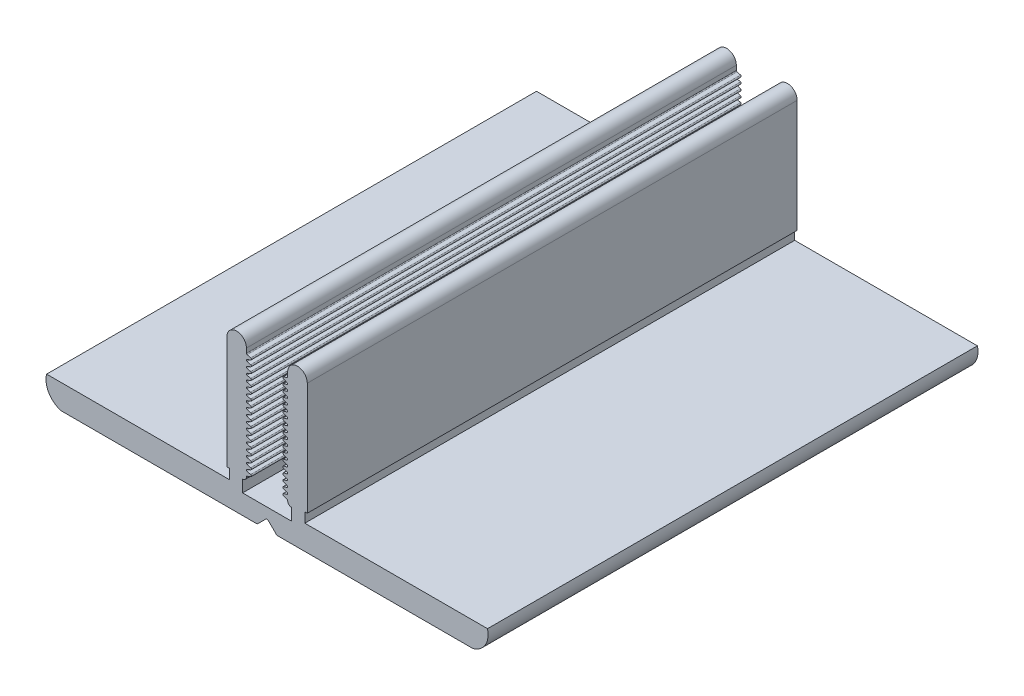
SolidWorks part; units mm, degrees
ref_plane "Спереди" through (0, 0, 0) normal (0, 0, 1) x (1, 0, 0)
ref_plane "Сверху" through (0, 0, 0) normal (0, 1, 0) x (1, 0, 0)
ref_plane "Справа" through (0, 0, 0) normal (1, 0, 0) x (0, 0, -1)
sketch "Эскиз1" plane through (0, 0, 0) normal (0, 0, 1) x (1, 0, 0)
  line L12 (1.5975, 2) -> (6.5975, 2)
  line L80 (3.9561, 0.8586) -> (3.1561, 0.0586)
  line L100 (2.0661, 10.8085) -> (2.4215, 10.7114)
  line L101 (2.0604, 10.384) -> (2.43, 10.5212)
  line L102 (2.0604, 10.9909) -> (2.43, 11.1281)
  line L104 (2.0604, 12.8116) -> (2.43, 12.9488)
  line L105 (2.0661, 11.4154) -> (2.4215, 11.3183)
  line L107 (3.0147, 0) -> (-9.305, 0)
  line L108 (2.0661, 7.774) -> (2.4215, 7.6769)
  line L109 (2.0604, 7.9564) -> (2.43, 8.0936)
  line L110 (2.0661, 8.3809) -> (2.4215, 8.2838)
  line L111 (2.0661, 10.2016) -> (2.4215, 10.1045)
  line L112 (2.0661, 8.9878) -> (2.4215, 8.8907)
  line L113 (2.0604, 8.5633) -> (2.43, 8.7005)
  line L114 (2.0604, 9.1702) -> (2.43, 9.3074)
  line L115 (2.0604, 9.7771) -> (2.43, 9.9143)
  line L116 (2.0661, 9.5947) -> (2.4215, 9.4976)
  line L117 (2.0661, 4.1326) -> (2.4215, 4.0355)
  line L118 (2.0604, 3.7081) -> (2.43, 3.8453)
  line L119 (2.0604, 4.315) -> (2.43, 4.4522)
  line L120 (2.0661, 4.7395) -> (2.4215, 4.6424)
  line L121 (2.0661, 5.3464) -> (2.4215, 5.2493)
  line L122 (2.0604, 5.5288) -> (2.43, 5.666)
  line L123 (2.0661, 5.9533) -> (2.4215, 5.8562)
  line L124 (2.0604, 4.9219) -> (2.43, 5.0591)
  line L125 (2.0661, 6.5602) -> (2.4215, 6.4631)
  line L126 (2.0604, 6.7426) -> (2.43, 6.8798)
  line L127 (2.0604, 6.1357) -> (2.43, 6.2729)
  line L128 (2.0604, 7.3495) -> (2.43, 7.4867)
  line L129 (2.0661, 7.1671) -> (2.4215, 7.07)
  line L130 (1.5975, 3.22) -> (1.5975, 2)
  line L131 (-0.0073, 3.5056) -> (0.2427, 3.5056)
  line L132 (0.2427, 3.5056) -> (0.2427, 2.5)
  line L135 (-0.0073, 3.5056) -> (-0.0073, 15)
  line L136 (2.0604, 13.4185) -> (2.43, 13.5557)
  line L138 (-16.9025, 0) -> (-9.305, 0)
  line L140 (2.0661, 13.843) -> (2.4215, 13.7459)
  line L141 (1.9927, 15) -> (1.9927, 14.5393)
  line L142 (2.0661, 12.0223) -> (2.4215, 11.9252)
  line L143 (2.0661, 14.4499) -> (2.4215, 14.3528)
  line L144 (2.0604, 14.0254) -> (2.43, 14.1626)
  line L145 (2.0604, 11.5978) -> (2.43, 11.735)
  line L146 (2.0661, 12.6292) -> (2.4215, 12.5321)
  line L147 (2.0661, 13.2361) -> (2.4215, 13.139)
  line L148 (2.0604, 12.2047) -> (2.43, 12.3419)
  line L149 (4.2389, 0.8586) -> (5.0389, 0.0586)
  line L150 (6.1346, 12.2047) -> (5.765, 12.3419)
  line L151 (6.1289, 13.2361) -> (5.7735, 13.139)
  line L152 (6.1289, 12.6292) -> (5.7735, 12.5321)
  line L153 (6.1346, 11.5978) -> (5.765, 11.735)
  line L154 (6.1346, 14.0254) -> (5.765, 14.1626)
  line L155 (6.1289, 14.4499) -> (5.7735, 14.3528)
  line L156 (6.1289, 12.0223) -> (5.7735, 11.9252)
  line L157 (6.2023, 15) -> (6.2023, 14.5393)
  line L158 (6.1289, 13.843) -> (5.7735, 13.7459)
  line L159 (6.1346, 13.4185) -> (5.765, 13.5557)
  line L160 (8.2023, 3.5056) -> (8.2023, 15)
  line L161 (7.9523, 3.5056) -> (7.9523, 2.5)
  line L162 (8.2023, 3.5056) -> (7.9523, 3.5056)
  line L163 (6.5975, 3.22) -> (6.5975, 2)
  line L164 (6.1289, 7.1671) -> (5.7735, 7.07)
  line L165 (6.1346, 7.3495) -> (5.765, 7.4867)
  line L166 (6.1346, 6.1357) -> (5.765, 6.2729)
  line L167 (6.1346, 6.7426) -> (5.765, 6.8798)
  line L168 (6.1289, 6.5602) -> (5.7735, 6.4631)
  line L169 (6.1346, 4.9219) -> (5.765, 5.0591)
  line L170 (6.1289, 5.9533) -> (5.7735, 5.8562)
  line L171 (6.1346, 5.5288) -> (5.765, 5.666)
  line L172 (6.1289, 5.3464) -> (5.7735, 5.2493)
  line L173 (6.1289, 4.7395) -> (5.7735, 4.6424)
  line L174 (6.1346, 4.315) -> (5.765, 4.4522)
  line L175 (6.1346, 3.7081) -> (5.765, 3.8453)
  line L176 (6.1289, 4.1326) -> (5.7735, 4.0355)
  line L177 (6.1289, 9.5947) -> (5.7735, 9.4976)
  line L178 (6.1346, 9.7771) -> (5.765, 9.9143)
  line L179 (6.1346, 9.1702) -> (5.765, 9.3074)
  line L180 (6.1346, 8.5633) -> (5.765, 8.7005)
  line L181 (6.1289, 8.9878) -> (5.7735, 8.8907)
  line L182 (6.1289, 10.2016) -> (5.7735, 10.1045)
  line L183 (6.1289, 8.3809) -> (5.7735, 8.2838)
  line L184 (6.1346, 7.9564) -> (5.765, 8.0936)
  line L185 (6.1289, 7.774) -> (5.7735, 7.6769)
  line L187 (6.1289, 11.4154) -> (5.7735, 11.3183)
  line L188 (6.1346, 12.8116) -> (5.765, 12.9488)
  line L189 (6.1346, 10.9909) -> (5.765, 11.1281)
  line L190 (6.1346, 10.384) -> (5.765, 10.5212)
  line L191 (6.1289, 10.8085) -> (5.7735, 10.7114)
  line L192 (25.0975, 0) -> (17.5, 0)
  line L195 (5.1803, 0) -> (17.5, 0)
  line L197 (10.7643, 2.5) -> (7.9523, 2.5)
  line L198 (10.7643, 2.5) -> (26.5975, 2.5)
  line L199 (0.2427, 2.5) -> (-18.4025, 2.5)
  arc A91 (4.2389, 0.8586) -> (3.9561, 0.8586) centre (4.0975, 0.7172) ccw
  arc A94 (2.43, 3.8453) -> (2.4215, 4.0355) centre (2.3952, 3.939) ccw
  arc A95 (2.43, 4.4522) -> (2.4215, 4.6424) centre (2.3952, 4.5459) ccw
  arc A96 (2.43, 5.0591) -> (2.4215, 5.2493) centre (2.3952, 5.1528) ccw
  arc A97 (3.0147, 0) -> (3.1561, 0.0586) centre (3.0147, 0.2) ccw
  arc A98 (2.43, 7.4867) -> (2.4215, 7.6769) centre (2.3952, 7.5804) ccw
  arc A99 (2.43, 8.0936) -> (2.4215, 8.2838) centre (2.3952, 8.1873) ccw
  arc A100 (1.9927, 10.8979) -> (2.0604, 10.9909) centre (2.0965, 10.8935) cw
  arc A101 (2.43, 10.5212) -> (2.4215, 10.7114) centre (2.3952, 10.6149) ccw
  arc A102 (2.0661, 10.8085) -> (1.9927, 10.8979) centre (2.0924, 10.905) cw
  arc A103 (2.43, 9.9143) -> (2.4215, 10.1045) centre (2.3952, 10.008) ccw
  arc A104 (2.43, 9.3074) -> (2.4215, 9.4976) centre (2.3952, 9.4011) ccw
  arc A105 (2.43, 8.7005) -> (2.4215, 8.8907) centre (2.3952, 8.7942) ccw
  arc A106 (2.0661, 11.4154) -> (1.9927, 11.5048) centre (2.0924, 11.5119) cw
  arc A107 (2.43, 11.1281) -> (2.4215, 11.3183) centre (2.3952, 11.2218) ccw
  arc A108 (2.43, 5.666) -> (2.4215, 5.8562) centre (2.3952, 5.7597) ccw
  arc A109 (2.43, 6.2729) -> (2.4215, 6.4631) centre (2.3952, 6.3666) ccw
  arc A110 (2.43, 6.8798) -> (2.4215, 7.07) centre (2.3952, 6.9735) ccw
  arc A113 (2.0661, 7.774) -> (1.9927, 7.8634) centre (2.0924, 7.8705) cw
  arc A114 (2.0661, 8.3809) -> (1.9927, 8.4703) centre (2.0924, 8.4774) cw
  arc A115 (1.9927, 7.8634) -> (2.0604, 7.9564) centre (2.0965, 7.859) cw
  arc A116 (2.0661, 9.5947) -> (1.9927, 9.6841) centre (2.0924, 9.6912) cw
  arc A117 (2.0661, 8.9878) -> (1.9927, 9.0772) centre (2.0924, 9.0843) cw
  arc A118 (1.9927, 9.0772) -> (2.0604, 9.1702) centre (2.0965, 9.0728) cw
  arc A119 (2.0661, 10.2016) -> (1.9927, 10.291) centre (2.0924, 10.2981) cw
  arc A120 (1.9927, 8.4703) -> (2.0604, 8.5633) centre (2.0965, 8.4659) cw
  arc A121 (1.9927, 10.291) -> (2.0604, 10.384) centre (2.0965, 10.2866) cw
  arc A122 (1.9927, 9.6841) -> (2.0604, 9.7771) centre (2.0965, 9.6797) cw
  arc A123 (1.9927, 3.6152) -> (1.5975, 3.22) centre (1.5975, 3.6152) cw
  arc A124 (2.0661, 4.1326) -> (1.9927, 4.2221) centre (2.0924, 4.2291) cw
  arc A125 (1.9927, 3.6152) -> (2.0604, 3.7081) centre (2.0965, 3.6107) cw
  arc A126 (1.9927, 4.2221) -> (2.0604, 4.315) centre (2.0965, 4.2176) cw
  arc A127 (2.0661, 4.7395) -> (1.9927, 4.829) centre (2.0924, 4.836) cw
  arc A128 (1.9927, 5.4359) -> (2.0604, 5.5288) centre (2.0965, 5.4314) cw
  arc A129 (2.0661, 5.3464) -> (1.9927, 5.4359) centre (2.0924, 5.4429) cw
  arc A130 (2.0661, 5.9533) -> (1.9927, 6.0428) centre (2.0924, 6.0498) cw
  arc A131 (1.9927, 4.829) -> (2.0604, 4.9219) centre (2.0965, 4.8245) cw
  arc A132 (1.9927, 6.6497) -> (2.0604, 6.7426) centre (2.0965, 6.6452) cw
  arc A133 (1.9927, 6.0428) -> (2.0604, 6.1357) centre (2.0965, 6.0383) cw
  arc A134 (2.0661, 6.5602) -> (1.9927, 6.6497) centre (2.0924, 6.6567) cw
  arc A135 (1.9927, 7.2566) -> (2.0604, 7.3495) centre (2.0965, 7.2521) cw
  arc A136 (2.0661, 7.1671) -> (1.9927, 7.2566) centre (2.0924, 7.2636) cw
  arc A138 (-0.0073, 15) -> (1.9927, 15) centre (0.9927, 15) cw
  arc A139 (1.9927, 11.5048) -> (2.0604, 11.5978) centre (2.0965, 11.5004) cw
  arc A140 (2.43, 14.1626) -> (2.4215, 14.3528) centre (2.3952, 14.2563) ccw
  arc A141 (2.0661, 12.0223) -> (1.9927, 12.1117) centre (2.0924, 12.1188) cw
  arc A142 (2.0661, 13.2361) -> (1.9927, 13.3255) centre (2.0924, 13.3326) cw
  arc A143 (2.43, 13.5557) -> (2.4215, 13.7459) centre (2.3952, 13.6494) ccw
  arc A144 (2.0661, 12.6292) -> (1.9927, 12.7186) centre (2.0924, 12.7257) cw
  arc A145 (2.43, 11.735) -> (2.4215, 11.9252) centre (2.3952, 11.8287) ccw
  arc A146 (1.9927, 12.1117) -> (2.0604, 12.2047) centre (2.0965, 12.1073) cw
  arc A147 (1.9927, 13.3255) -> (2.0604, 13.4185) centre (2.0965, 13.3211) cw
  arc A148 (1.9927, 12.7186) -> (2.0604, 12.8116) centre (2.0965, 12.7142) cw
  arc A149 (2.0661, 14.4499) -> (1.9927, 14.5393) centre (2.0924, 14.5464) cw
  arc A150 (2.43, 12.9488) -> (2.4215, 13.139) centre (2.3952, 13.0425) ccw
  arc A151 (2.43, 12.3419) -> (2.4215, 12.5321) centre (2.3952, 12.4356) ccw
  arc A152 (2.0661, 13.843) -> (1.9927, 13.9324) centre (2.0924, 13.9395) cw
  arc A153 (1.9927, 13.9324) -> (2.0604, 14.0254) centre (2.0965, 13.928) cw
  arc A154 (5.1803, 0) -> (5.0389, 0.0586) centre (5.1803, 0.2) cw
  arc A155 (6.2023, 13.9324) -> (6.1346, 14.0254) centre (6.0985, 13.928) ccw
  arc A156 (6.1289, 13.843) -> (6.2023, 13.9324) centre (6.1025, 13.9395) ccw
  arc A157 (5.765, 12.3419) -> (5.7735, 12.5321) centre (5.7998, 12.4356) cw
  arc A158 (5.765, 12.9488) -> (5.7735, 13.139) centre (5.7998, 13.0425) cw
  arc A159 (6.1289, 14.4499) -> (6.2023, 14.5393) centre (6.1025, 14.5464) ccw
  arc A160 (6.2023, 12.7186) -> (6.1346, 12.8116) centre (6.0985, 12.7142) ccw
  arc A161 (6.2023, 13.3255) -> (6.1346, 13.4185) centre (6.0985, 13.3211) ccw
  arc A162 (6.2023, 12.1117) -> (6.1346, 12.2047) centre (6.0985, 12.1073) ccw
  arc A163 (5.765, 11.735) -> (5.7735, 11.9252) centre (5.7998, 11.8287) cw
  arc A164 (6.1289, 12.6292) -> (6.2023, 12.7186) centre (6.1025, 12.7257) ccw
  arc A165 (5.765, 13.5557) -> (5.7735, 13.7459) centre (5.7998, 13.6494) cw
  arc A166 (6.1289, 13.2361) -> (6.2023, 13.3255) centre (6.1025, 13.3326) ccw
  arc A167 (6.1289, 12.0223) -> (6.2023, 12.1117) centre (6.1025, 12.1188) ccw
  arc A168 (5.765, 14.1626) -> (5.7735, 14.3528) centre (5.7998, 14.2563) cw
  arc A169 (6.2023, 11.5048) -> (6.1346, 11.5978) centre (6.0985, 11.5004) ccw
  arc A170 (8.2023, 15) -> (6.2023, 15) centre (7.2023, 15) ccw
  arc A171 (6.1289, 7.1671) -> (6.2023, 7.2566) centre (6.1025, 7.2636) ccw
  arc A172 (6.2023, 7.2566) -> (6.1346, 7.3495) centre (6.0985, 7.2521) ccw
  arc A173 (6.1289, 6.5602) -> (6.2023, 6.6497) centre (6.1025, 6.6567) ccw
  arc A174 (6.2023, 6.0428) -> (6.1346, 6.1357) centre (6.0985, 6.0383) ccw
  arc A175 (6.2023, 6.6497) -> (6.1346, 6.7426) centre (6.0985, 6.6452) ccw
  arc A176 (6.2023, 4.829) -> (6.1346, 4.9219) centre (6.0985, 4.8245) ccw
  arc A177 (6.1289, 5.9533) -> (6.2023, 6.0428) centre (6.1025, 6.0498) ccw
  arc A178 (6.1289, 5.3464) -> (6.2023, 5.4359) centre (6.1025, 5.4429) ccw
  arc A179 (6.2023, 5.4359) -> (6.1346, 5.5288) centre (6.0985, 5.4314) ccw
  arc A180 (6.1289, 4.7395) -> (6.2023, 4.829) centre (6.1025, 4.836) ccw
  arc A181 (6.2023, 4.2221) -> (6.1346, 4.315) centre (6.0985, 4.2176) ccw
  arc A182 (6.2023, 3.6152) -> (6.1346, 3.7081) centre (6.0985, 3.6107) ccw
  arc A183 (6.1289, 4.1326) -> (6.2023, 4.2221) centre (6.1025, 4.2291) ccw
  arc A184 (6.2023, 3.6152) -> (6.5975, 3.22) centre (6.5975, 3.6152) ccw
  arc A185 (6.2023, 9.6841) -> (6.1346, 9.7771) centre (6.0985, 9.6797) ccw
  arc A186 (6.2023, 10.291) -> (6.1346, 10.384) centre (6.0985, 10.2866) ccw
  arc A187 (6.2023, 8.4703) -> (6.1346, 8.5633) centre (6.0985, 8.4659) ccw
  arc A188 (6.1289, 10.2016) -> (6.2023, 10.291) centre (6.1025, 10.2981) ccw
  arc A189 (6.2023, 9.0772) -> (6.1346, 9.1702) centre (6.0985, 9.0728) ccw
  arc A190 (6.1289, 8.9878) -> (6.2023, 9.0772) centre (6.1025, 9.0843) ccw
  arc A191 (6.1289, 9.5947) -> (6.2023, 9.6841) centre (6.1025, 9.6912) ccw
  arc A192 (6.2023, 7.8634) -> (6.1346, 7.9564) centre (6.0985, 7.859) ccw
  arc A193 (6.1289, 8.3809) -> (6.2023, 8.4703) centre (6.1025, 8.4774) ccw
  arc A194 (6.1289, 7.774) -> (6.2023, 7.8634) centre (6.1025, 7.8705) ccw
  arc A195 (5.765, 6.8798) -> (5.7735, 7.07) centre (5.7998, 6.9735) cw
  arc A196 (5.765, 6.2729) -> (5.7735, 6.4631) centre (5.7998, 6.3666) cw
  arc A197 (5.765, 5.666) -> (5.7735, 5.8562) centre (5.7998, 5.7597) cw
  arc A198 (5.765, 11.1281) -> (5.7735, 11.3183) centre (5.7998, 11.2218) cw
  arc A199 (6.1289, 11.4154) -> (6.2023, 11.5048) centre (6.1025, 11.5119) ccw
  arc A200 (5.765, 8.7005) -> (5.7735, 8.8907) centre (5.7998, 8.7942) cw
  arc A201 (5.765, 9.3074) -> (5.7735, 9.4976) centre (5.7998, 9.4011) cw
  arc A202 (5.765, 9.9143) -> (5.7735, 10.1045) centre (5.7998, 10.008) cw
  arc A203 (6.1289, 10.8085) -> (6.2023, 10.8979) centre (6.1025, 10.905) ccw
  arc A204 (5.765, 10.5212) -> (5.7735, 10.7114) centre (5.7998, 10.6149) cw
  arc A205 (6.2023, 10.8979) -> (6.1346, 10.9909) centre (6.0985, 10.8935) ccw
  arc A206 (5.765, 8.0936) -> (5.7735, 8.2838) centre (5.7998, 8.1873) cw
  arc A207 (5.765, 7.4867) -> (5.7735, 7.6769) centre (5.7998, 7.5804) cw
  arc A208 (5.765, 5.0591) -> (5.7735, 5.2493) centre (5.7998, 5.1528) cw
  arc A209 (5.765, 4.4522) -> (5.7735, 4.6424) centre (5.7998, 4.5459) cw
  arc A210 (5.765, 3.8453) -> (5.7735, 4.0355) centre (5.7998, 3.939) cw
  arc A212 (26.5975, 2.5) -> (25.0975, 0) centre (24.5975, 2) cw
  arc A213 (-18.4025, 2.5) -> (-16.9025, 0) centre (-16.4025, 2) ccw
  point P75 (7, 10.9962)
  point P77 (1.195, 10.9962)
  point P329 (4.0975, 2)
extrude "Бобышка-Вытянуть2" add sketch "Эскиз1" along normal blind 50
